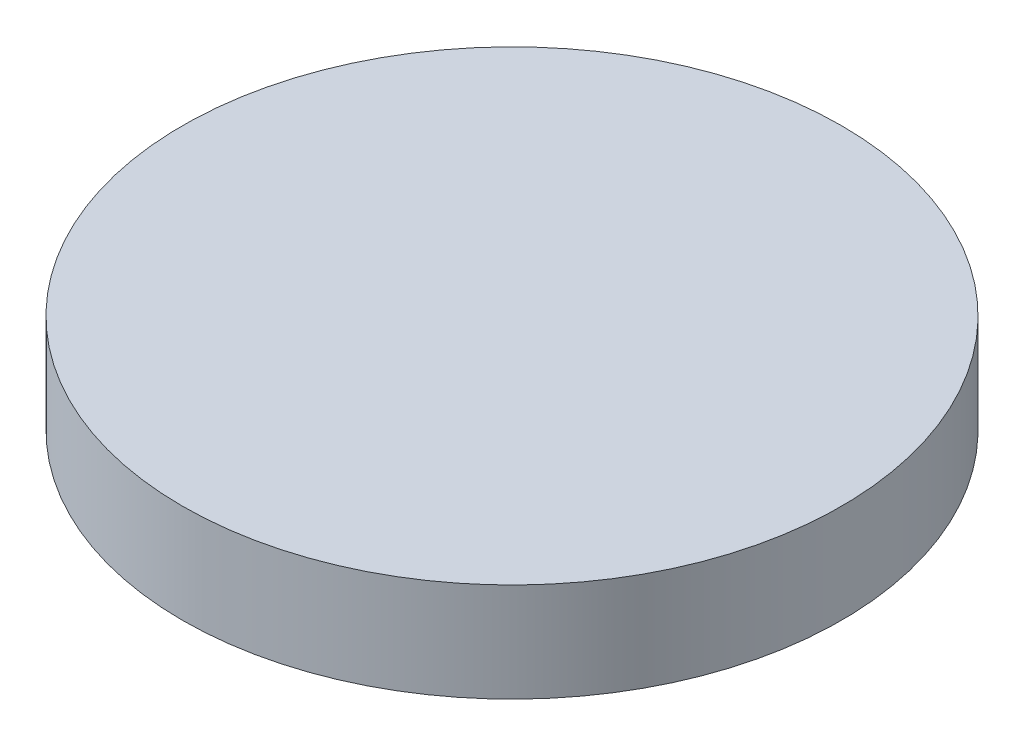
SolidWorks part; units mm, degrees
ref_plane "Front Plane" through (0, 0, 0) normal (0, 0, 1) x (1, 0, 0)
ref_plane "Top Plane" through (0, 0, 0) normal (0, 1, 0) x (1, 0, 0)
ref_plane "Right Plane" through (0, 0, 0) normal (1, 0, 0) x (0, 0, -1)
sketch "Sketch1" plane through (0, 0, 0) normal (0, 1, 0) x (1, 0, 0)
  circle A0 centre (0, 0) radius 5
  dimension "D1" = 10
extrude "Boss-Extrude1" add sketch "Sketch1" along normal blind 1.5
sketch "Sketch2" plane through (0, 0, 0) normal (0, -1, 0) x (1, 0, 0)
  circle A0 centre (0, 0) radius 4.5
  dimension "D1" = 9
extrude "Boss-Extrude2" add sketch "Sketch2" along normal blind 0.1
